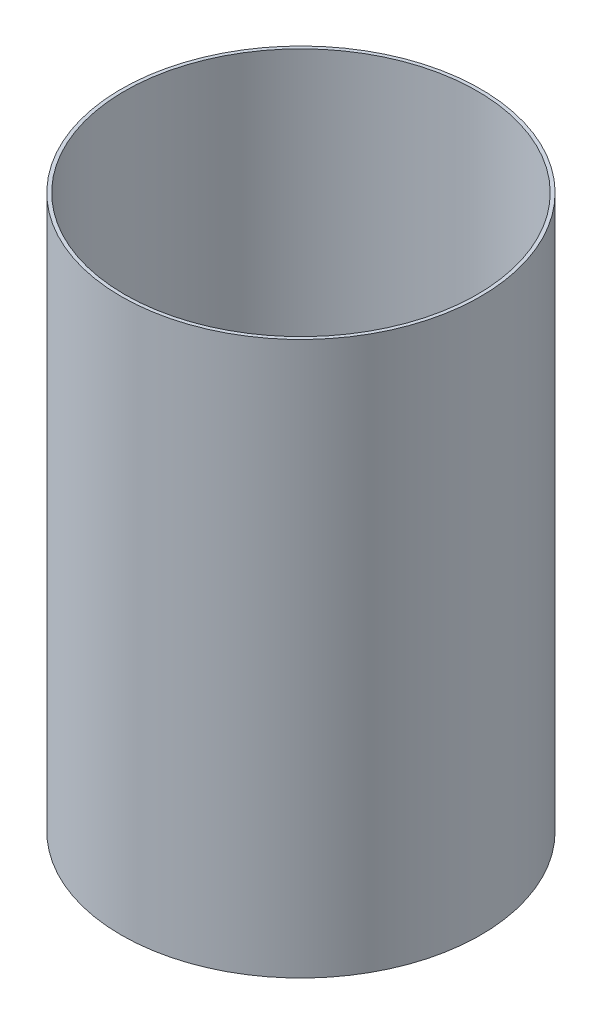
SolidWorks part; units mm, degrees
material "E-Glass Fiber"
ref_plane "Front Plane" through (0, 0, 0) normal (0, 0, 1) x (1, 0, 0)
ref_plane "Top Plane" through (0, 0, 0) normal (0, 1, 0) x (1, 0, 0)
ref_plane "Right Plane" through (0, 0, 0) normal (1, 0, 0) x (0, 0, -1)
sketch "Sketch1" plane through (0, 0, 0) normal (0, 1, 0) x (1, 0, 0)
  circle A0 centre (0, 0) radius 66.04
  circle A1 centre (0, 0) radius 64.77
  dimension "D1" = 132.08
  dimension "D2" = 129.54
extrude "Boss-Extrude1" add sketch "Sketch1" along normal blind 203.2
